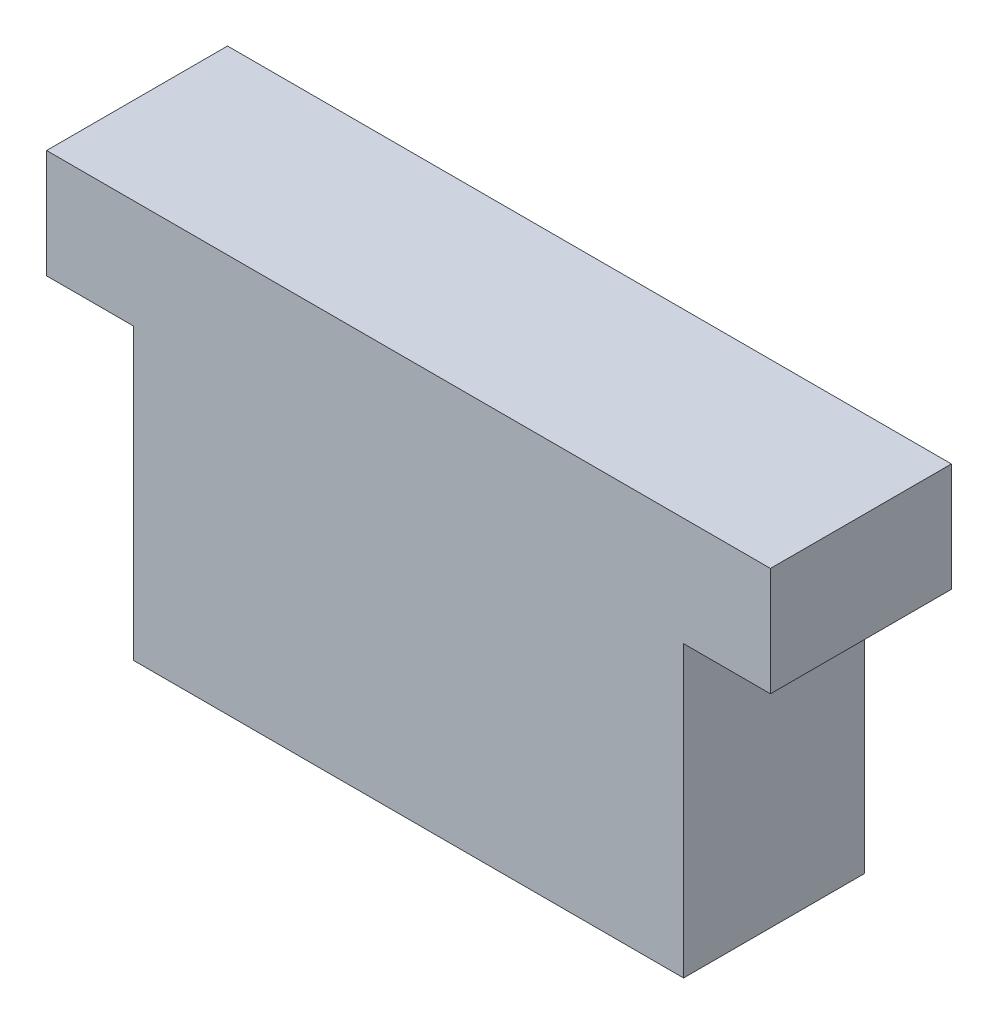
SolidWorks part; units mm, degrees
ref_plane "前视基准面" through (0, 0, 0) normal (0, 0, 1) x (1, 0, 0)
ref_plane "上视基准面" through (0, 0, 0) normal (0, 1, 0) x (1, 0, 0)
ref_plane "右视基准面" through (0, 0, 0) normal (1, 0, 0) x (0, 0, -1)
sketch "草图1" plane through (0, 0, 0) normal (0, 0, 1) x (1, 0, 0)
  line L1 (-10, -1.5) -> (10, -1.5)
  line L2 (-10, -1.5) -> (-10, 1.5)
  line L3 (-10, 1.5) -> (10, 1.5)
  line L4 (10, -1.5) -> (10, 1.5)
  line L5 (-10, -1.5) -> (10, 1.5) construction
  line L6 (-10, 1.5) -> (10, -1.5) construction
  line L7 (-7.6, -1.5) -> (7.6, -1.5)
  line L8 (-7.6, -1.5) -> (-7.6, -9.5)
  line L9 (-7.6, -9.5) -> (7.6, -9.5)
  line L10 (7.6, -1.5) -> (7.6, -9.5)
  line L11 (-7.6, -1.5) -> (7.6, -9.5) construction
  line L12 (-7.6, -9.5) -> (7.6, -1.5) construction
  point P0 (0, 0)
  point P5 (0, -5.5)
  dimension "D1" = 3
  dimension "D2" = 20
  dimension "D3" = 15.2
  dimension "D4" = 8
extrude "凸台-拉伸1" add sketch "草图1" along normal blind 5 contours L1 L4 L3 L2 | L10 L1 L8 L9
